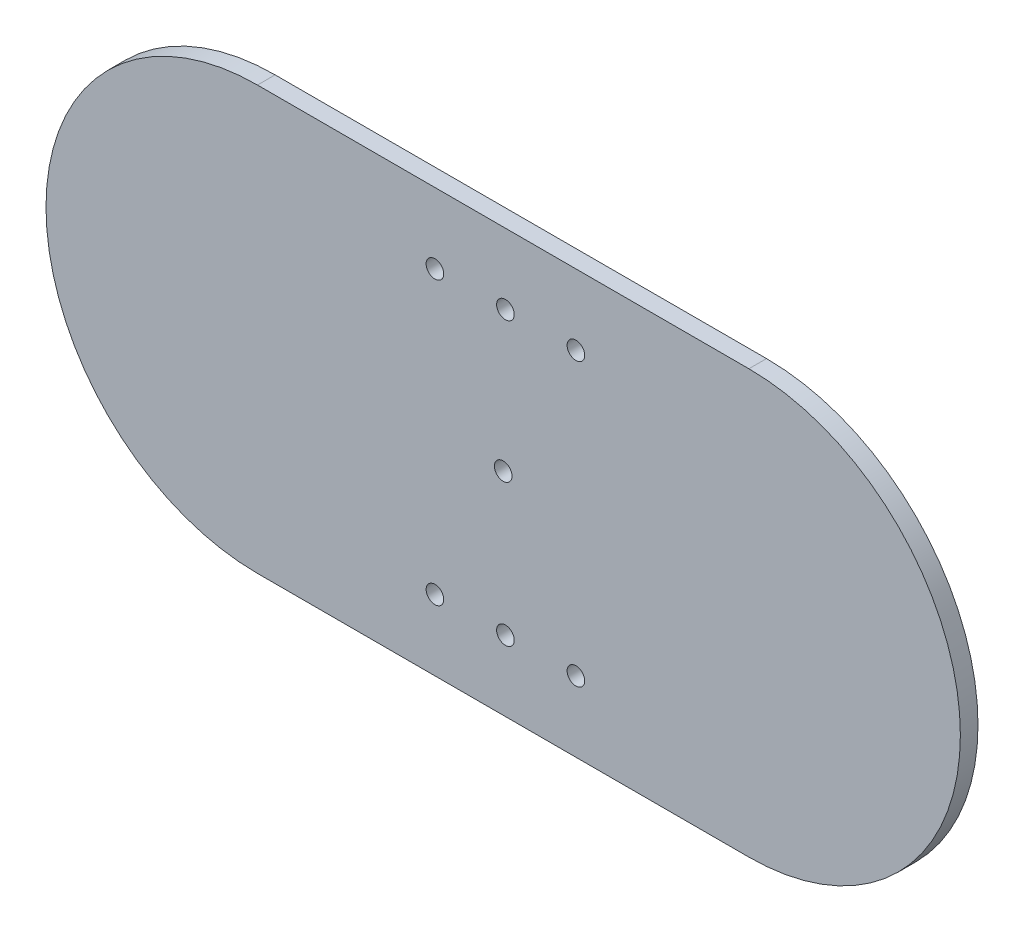
SolidWorks part; units mm, degrees
ref_plane "Front Plane" through (0, 0, 0) normal (0, 0, 1) x (1, 0, 0)
ref_plane "Top Plane" through (0, 0, 0) normal (0, 1, 0) x (1, 0, 0)
ref_plane "Right Plane" through (0, 0, 0) normal (1, 0, 0) x (0, 0, -1)
sketch "Sketch1" plane through (0, 0, 0) normal (0, 0, 1) x (1, 0, 0)
  line L0 (-81.1545, 0) -> (95.9099, 0) construction
  line L1 (-81.1545, 76.2) -> (95.9099, 76.2)
  line L2 (-81.1545, -76.2) -> (95.9099, -76.2)
  line L3 (-81.1545, 0) -> (95.9099, 0) construction
  line L4 (-81.1545, 63.5) -> (95.9099, 63.5) construction
  line L5 (-81.1545, -63.5) -> (95.9099, -63.5) construction
  arc A0 (-81.1545, 76.2) -> (-81.1545, -76.2) centre (-81.1545, 0) ccw
  arc A1 (95.9099, -76.2) -> (95.9099, 76.2) centre (95.9099, 0) ccw
  arc A2 (-81.1545, 63.5) -> (-81.1545, -63.5) centre (-81.1545, 0) ccw construction
  arc A3 (95.9099, -63.5) -> (95.9099, 63.5) centre (95.9099, 0) ccw construction
  circle A4 centre (8.1842, 50.8) radius 3.175
  circle A5 centre (8.1842, -50.8) radius 3.175
  circle A6 centre (-17.2158, 50.8) radius 3.175
  circle A7 centre (33.5842, 50.8) radius 3.175
  circle A8 centre (33.5842, -50.8) radius 3.175
  circle A9 centre (-17.2158, -50.8) radius 3.175
  circle A10 centre (7.3777, 0) radius 3.175
  point P3 (7.3777, 0)
  point P10 (7.3777, 0)
  point P28 (7.3777, 0)
  dimension "D3" = 6.35
  dimension "D5" = 6.35
  dimension "D1" = 152.4
  dimension "D2" = 127
  dimension "D4" = 12.7
  dimension "D6" = 25.4
  dimension "D7" = 25.4
  dimension "D8" = 12.7
extrude "Boss-Extrude1" add sketch "Sketch1" along normal blind 6.35
sketch "Sketch2" plane through (0, 0, 6.35) normal (0, 0, 1) x (1, 0, 0)
  point P0 (7.3777, 0)
